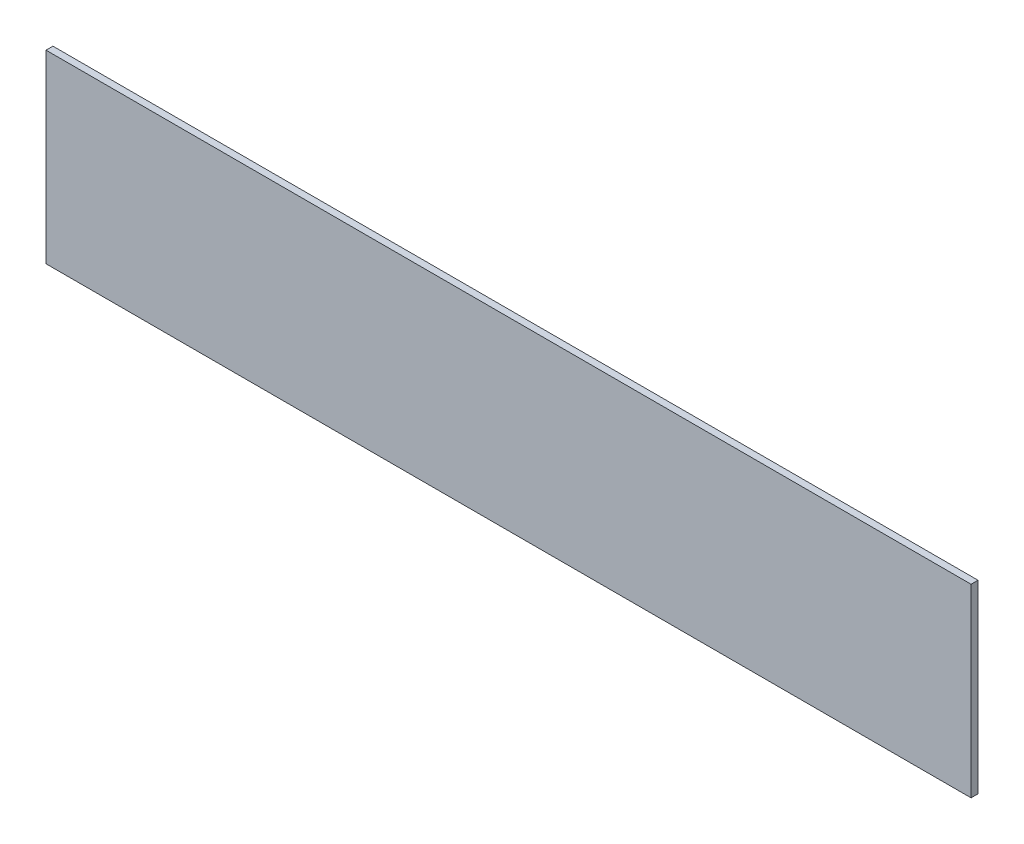
SolidWorks part; units mm, degrees
ref_plane "Front Plane" through (0, 0, 0) normal (0, 0, 1) x (1, 0, 0)
ref_plane "Top Plane" through (0, 0, 0) normal (0, 1, 0) x (1, 0, 0)
ref_plane "Right Plane" through (0, 0, 0) normal (1, 0, 0) x (0, 0, -1)
sketch "Sketch1" plane through (0, 0, 0) normal (0, 0, 1) x (1, 0, 0)
  line L1 (-635, 127) -> (635, 127)
  line L2 (-635, 127) -> (-635, -127)
  line L3 (-635, -127) -> (635, -127)
  line L4 (635, 127) -> (635, -127)
  line L5 (-635, 127) -> (635, -127) construction
  line L6 (-635, -127) -> (635, 127) construction
  point P0 (0, 0)
  dimension "D1" = 254
  dimension "D2" = 1270
extrude "Boss-Extrude1" add sketch "Sketch1" along normal blind 9.525
